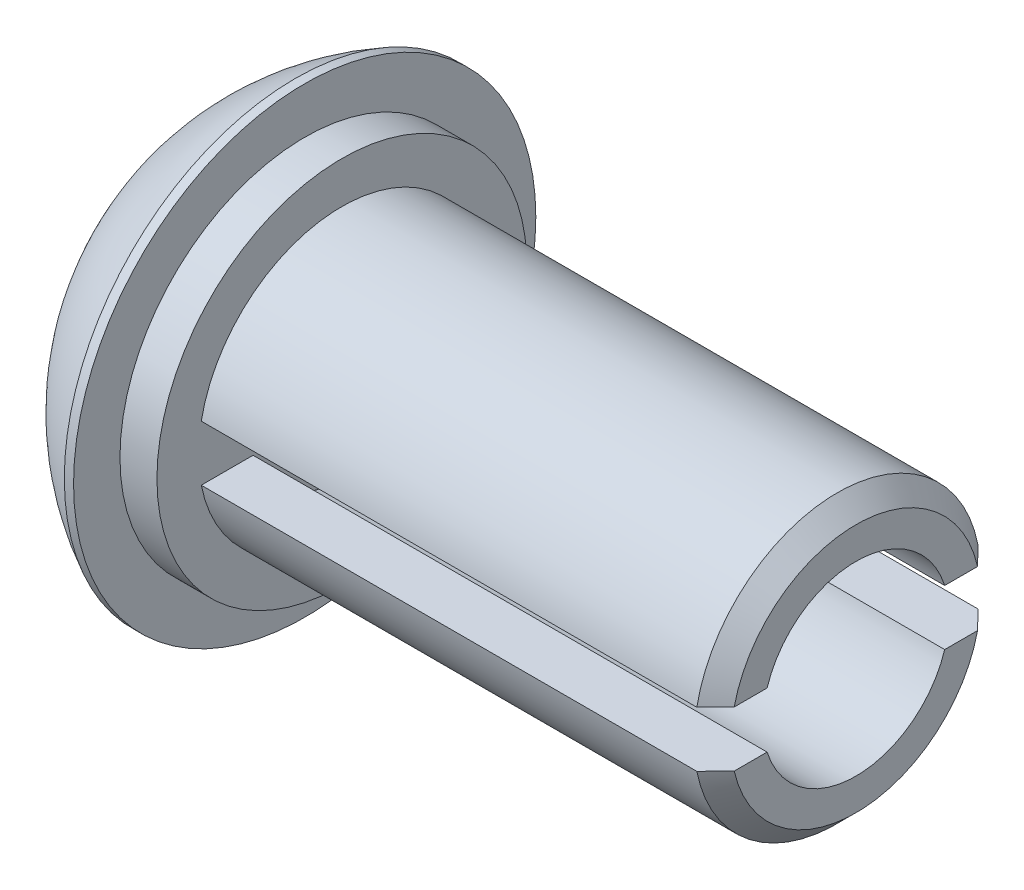
SolidWorks part; units mm, degrees
material "PVC Rigid"
ref_plane "Front Plane" through (0, 0, 0) normal (0, 0, 1) x (1, 0, 0)
ref_plane "Top Plane" through (0, 0, 0) normal (0, 1, 0) x (1, 0, 0)
ref_plane "Right Plane" through (0, 0, 0) normal (1, 0, 0) x (0, 0, -1)
sketch "Sketch1" plane through (0, 0, 0) normal (0, 0, 1) x (1, 0, 0)
  line L0 (0, 0) -> (12.7, 0) construction
  line L1 (0, 0) -> (0, 4.0005) construction
  line L2 (1.9558, 3.175) -> (2.0828, 3.175)
  line L3 (2.0828, 3.175) -> (2.0828, 0.889)
  line L4 (2.0828, 0.889) -> (2.0853, 0.889)
  line L5 (2.0853, 0.889) -> (2.0853, 2.54)
  line L6 (2.0853, 2.54) -> (2.5933, 2.54)
  line L7 (2.5933, 2.54) -> (2.5933, 1.9685)
  line L8 (2.5933, 1.9685) -> (9.6545, 1.9685)
  line L9 (9.6545, 1.9685) -> (9.6545, 1.2778)
  line L10 (2.5933, 0) -> (0, 0)
  line L12 (2.5933, 1.2778) -> (9.6545, 1.2778)
  line L13 (2.5933, 1.2778) -> (2.5933, 0)
  arc A0 (0, 0) -> (1.9558, 3.175) centre (3.555, 0) cw
  dimension "D12" = 3.555
  dimension "D1" = 12.7
  dimension "D2" = 2.0828
  dimension "D3" = 0.508
  dimension "D4" = 0.0025
  dimension "D5" = 7.0612
  dimension "D6" = 3.937
  dimension "D7" = 6.35
  dimension "D8" = 5.08
  dimension "D9" = 1.778
  dimension "D10" = 0.6907
  dimension "D11" = 0.5715
  dimension "D13" = 0.127
revolve "Revolve1" add sketch "Sketch1" angle 360 about L0
chamfer "Chamfer1" distance 0.254 angle 45 1 edges at (9.6545, 0, 1.9685)
sketch "Sketch2" plane through (0, 0, 0) normal (0, 0, 1) x (1, 0, 0)
  line L0 (2.5933, -2.54) -> (2.5933, 2.54) construction
  line L1 (2.5933, 0.381) -> (9.6545, 0.381)
  line L2 (2.5933, 0.381) -> (2.5933, -0.381)
  line L3 (2.5933, -0.381) -> (9.6545, -0.381)
  line L4 (9.6545, 0.381) -> (9.6545, -0.381)
  line L5 (0, 0) -> (2.5933, 0) construction
  line L6 (9.6545, -1.7145) -> (9.6545, 1.7145) construction
  dimension "D1" = 0.762
extrude "Cut-Extrude1" cut sketch "Sketch2" against normal through all and the other way through all
